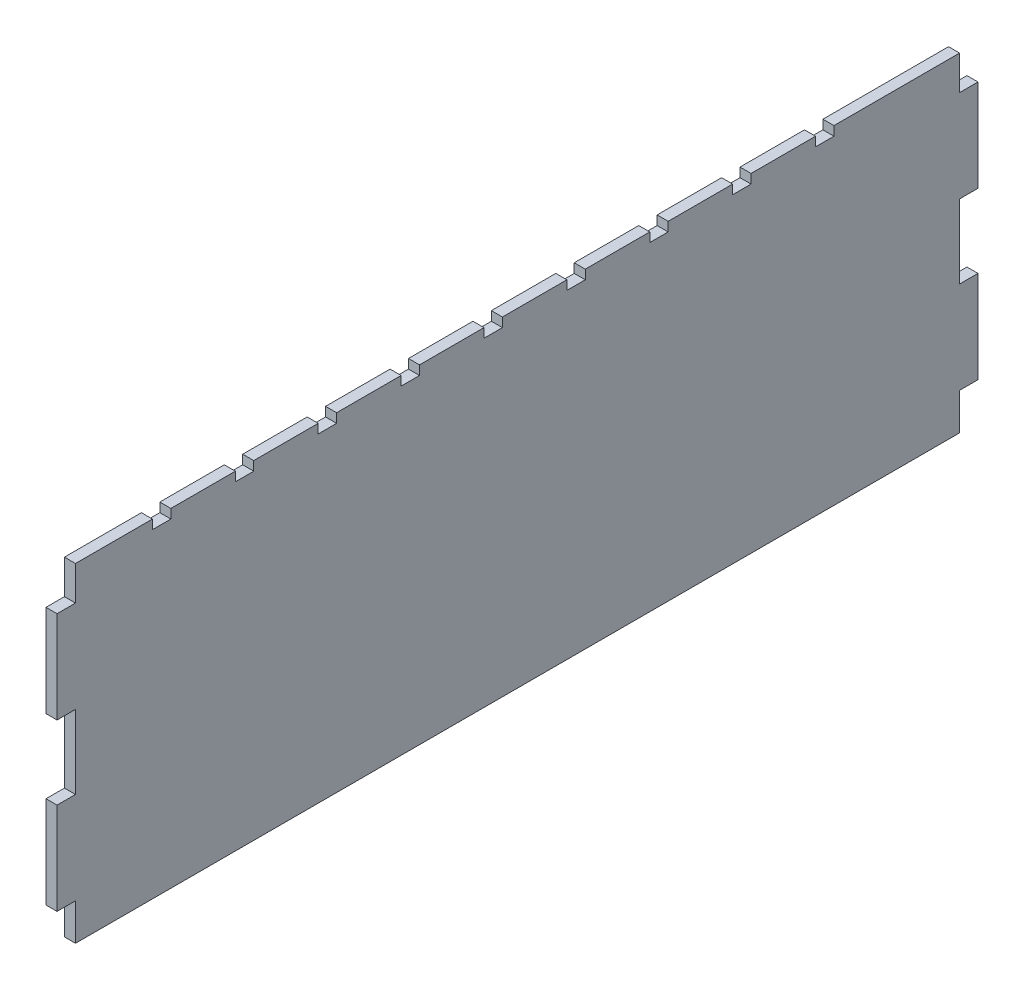
SolidWorks part; units mm, degrees
ref_plane "Спереди" through (0, 0, 0) normal (0, 0, 1) x (1, 0, 0)
ref_plane "Сверху" through (0, 0, 0) normal (0, 1, 0) x (1, 0, 0)
ref_plane "Справа" through (0, 0, 0) normal (1, 0, 0) x (0, 0, -1)
sketch "Эскиз1" plane through (0, 0, 0) normal (1, 0, 0) x (0, 0, -1)
  line L0 (-240, 0) -> (240, 0) construction
  line L1 (240, -90) -> (-240, -90)
  line L2 (250, -70) -> (250, -20)
  line L3 (240, 88.6) -> (171.7894, 88.6)
  line L4 (-250, -70) -> (-250, -20)
  line L5 (240, -86.4) -> (-240, 86.4) construction
  line L6 (240, 86.4) -> (-240, -86.4) construction
  line L7 (-250, 20) -> (-250, 70)
  line L8 (0, -123.0315) -> (0, 123.0315) construction
  line L9 (240, -20) -> (240, 20)
  line L10 (-250, 70) -> (-240, 70)
  line L11 (-240, 88.6) -> (-240, 70)
  line L12 (250, 20) -> (240, 20)
  line L13 (250, -20) -> (240, -20)
  line L14 (-250, -70) -> (-240, -70)
  line L15 (-240, -90) -> (-240, -70)
  line L16 (-250, -20) -> (-240, -20)
  line L17 (240, -90) -> (240, -70)
  line L18 (-250, 20) -> (-240, 20)
  line L19 (-240, -20) -> (-240, 20)
  line L20 (250, -70) -> (240, -70)
  line L21 (240, 88.6) -> (240, 70)
  line L22 (250, 70) -> (240, 70)
  line L23 (250, 20) -> (250, 70)
  line L24 (250, -70) -> (250, -20)
  line L25 (250, 20) -> (250, 70)
  line L26 (-240, 88.6) -> (-198.2106, 88.6) construction
  line L27 (-198.2106, 88.6) -> (-240, 88.6)
  line L28 (-143.2106, 88.6) -> (-143.2106, 83.6)
  line L29 (-188.2106, 88.6) -> (-188.2106, 83.6)
  line L30 (-188.2106, 83.6) -> (-198.2106, 83.6)
  line L31 (-198.2106, 88.6) -> (-198.2106, 83.6)
  line L32 (-143.2106, 83.6) -> (-153.2106, 83.6)
  line L33 (-153.2106, 88.6) -> (-153.2106, 83.6)
  line L34 (-98.2106, 88.6) -> (-98.2106, 83.6)
  line L35 (-98.2106, 83.6) -> (-108.2106, 83.6)
  line L36 (-108.2106, 88.6) -> (-108.2106, 83.6)
  line L37 (-53.2106, 88.6) -> (-53.2106, 83.6)
  line L38 (-53.2106, 83.6) -> (-63.2106, 83.6)
  line L39 (-63.2106, 88.6) -> (-63.2106, 83.6)
  line L40 (-8.2106, 88.6) -> (-8.2106, 83.6)
  line L41 (-8.2106, 83.6) -> (-18.2106, 83.6)
  line L42 (-18.2106, 88.6) -> (-18.2106, 83.6)
  line L43 (36.7894, 88.6) -> (36.7894, 83.6)
  line L44 (36.7894, 83.6) -> (26.7894, 83.6)
  line L45 (26.7894, 88.6) -> (26.7894, 83.6)
  line L46 (81.7894, 88.6) -> (81.7894, 83.6)
  line L47 (81.7894, 83.6) -> (71.7894, 83.6)
  line L48 (71.7894, 88.6) -> (71.7894, 83.6)
  line L49 (126.7894, 88.6) -> (126.7894, 83.6)
  line L50 (126.7894, 83.6) -> (116.7894, 83.6)
  line L51 (116.7894, 88.6) -> (116.7894, 83.6)
  line L52 (171.7894, 88.6) -> (171.7894, 83.6)
  line L53 (171.7894, 83.6) -> (161.7894, 83.6)
  line L54 (161.7894, 88.6) -> (161.7894, 83.6)
  line L55 (-153.2106, 88.6) -> (-188.2106, 88.6)
  line L56 (-108.2106, 88.6) -> (-143.2106, 88.6)
  line L57 (-63.2106, 88.6) -> (-98.2106, 88.6)
  line L58 (-18.2106, 88.6) -> (-53.2106, 88.6)
  line L59 (26.7894, 88.6) -> (-8.2106, 88.6)
  line L60 (71.7894, 88.6) -> (36.7894, 88.6)
  line L61 (116.7894, 88.6) -> (81.7894, 88.6)
  line L62 (161.7894, 88.6) -> (126.7894, 88.6)
  point P0 (0, 0)
  point P21 (0, 0)
  dimension "D1" = 9
extrude "Бобышка-Вытянуть2" add sketch "Эскиз1" along normal blind 6 contours L54 L62 L49 L50 L51 L61 L46 L47 L48 L60 L43 L44 L45 L59 L40 L41 L42 L58 L37 L38 L39 L57 L34 L35 L36 L56 L28 L32 L33 L55 L29 L30 L31 L27 L11 L10 L7 L18 L19 L16 L4 L14 L15 L1 L17 L20 L2 L13 L9 L12 L23
